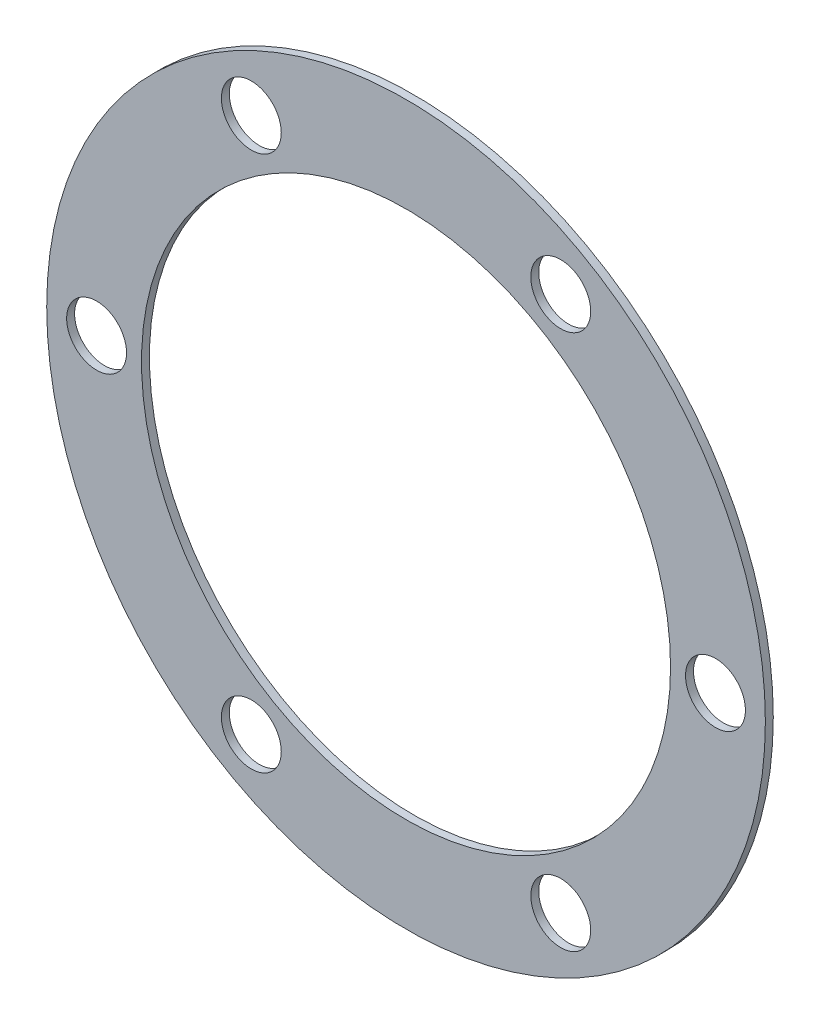
SolidWorks part; units mm, degrees
material "BUTYL"
ref_plane "Front Plane" through (0, 0, 0) normal (0, 0, 1) x (1, 0, 0)
ref_plane "Top Plane" through (0, 0, 0) normal (0, 1, 0) x (1, 0, 0)
ref_plane "Right Plane" through (0, 0, 0) normal (1, 0, 0) x (0, 0, -1)
sketch "Sketch1" plane through (0, 0, 0) normal (0, 0, 1) x (1, 0, 0)
  arc A0 (-1.586, 17.93) -> (-14.7349, 10.3385) centre (0, 0) ccw construction
  circle A1 centre (-15.5, 0) radius 1.5
  circle A2 centre (-7.75, 13.4234) radius 1.5
  circle A3 centre (7.75, 13.4234) radius 1.5
  circle A4 centre (15.5, 0) radius 1.5
  circle A5 centre (7.75, -13.4234) radius 1.5
  circle A6 centre (-7.75, -13.4234) radius 1.5
  arc A7 (-1.586, 17.93) -> (-14.7349, 10.3385) centre (0, 0) ccw
  arc A8 (-1.5846, 13.1549) -> (-10.6002, 7.9498) centre (0, 0) ccw
  arc A9 (-6.4162, 14.1097) -> (-9.0112, 12.6114) centre (0, 0) ccw construction
  arc A23 (14.7349, 10.3385) -> (1.586, 17.93) centre (0, 0) ccw construction
  arc A24 (14.7349, 10.3385) -> (1.586, 17.93) centre (0, 0) ccw
  arc A25 (-9.0112, -12.6114) -> (-6.4162, -14.1097) centre (0, 0) ccw construction
  arc A26 (16.3208, -7.5915) -> (16.3208, 7.5915) centre (0, 0) ccw construction
  arc A27 (16.3208, -7.5915) -> (16.3208, 7.5915) centre (0, 0) ccw
  arc A28 (12.1848, -5.2051) -> (12.1848, 5.2051) centre (0, 0) ccw
  arc A29 (-15.4274, 1.4982) -> (-15.4274, -1.4982) centre (0, 0) ccw construction
  arc A30 (1.586, -17.93) -> (14.7349, -10.3385) centre (0, 0) ccw construction
  arc A31 (1.586, -17.93) -> (14.7349, -10.3385) centre (0, 0) ccw
  arc A32 (1.5846, -13.1549) -> (10.6002, -7.9498) centre (0, 0) ccw
  arc A33 (-14.7349, -10.3385) -> (-1.586, -17.93) centre (0, 0) ccw construction
  arc A34 (-14.7349, -10.3385) -> (-1.586, -17.93) centre (0, 0) ccw
  arc A35 (-10.6002, -7.9498) -> (-1.5846, -13.1549) centre (0, 0) ccw
  arc A36 (-16.3208, 7.5915) -> (-16.3208, -7.5915) centre (0, 0) ccw construction
  arc A37 (-16.3208, 7.5915) -> (-16.3208, -7.5915) centre (0, 0) ccw
  arc A38 (-12.1848, 5.2051) -> (-12.1848, -5.2051) centre (0, 0) ccw
  arc A39 (10.6002, 7.9498) -> (1.5846, 13.1549) centre (0, 0) ccw
  circle A40 centre (0, 0) radius 13.25
  circle A41 centre (0, 0) radius 18
  dimension "D1" = 3
  dimension "D2" = 36
  dimension "D4" = 26.5
  dimension "D5" = 31
  dimension "D3" = 6
extrude "Boss-Extrude1" add sketch "Sketch1" along normal blind 0.3969 contours A0 A6 A5 A4 A3 A2 A1
